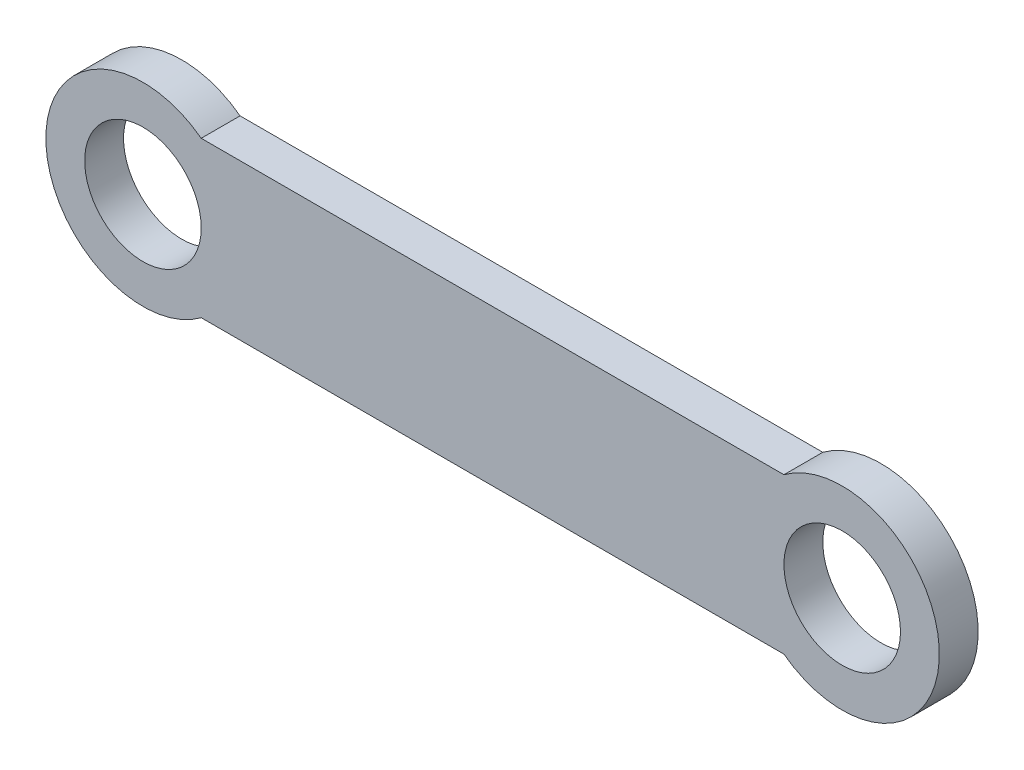
SolidWorks part; units mm, degrees
ref_plane "前视基准面" through (0, 0, 0) normal (0, 0, 1) x (1, 0, 0)
ref_plane "上视基准面" through (0, 0, 0) normal (0, 1, 0) x (1, 0, 0)
ref_plane "右视基准面" through (0, 0, 0) normal (1, 0, 0) x (0, 0, -1)
sketch "草图1" plane through (0, 0, 0) normal (0, 0, 1) x (1, 0, 0)
  line L1 (-29.9356, 0.5) -> (-14.9356, 0.5)
  line L3 (-29.9356, -3.5) -> (-14.9356, -3.5)
  arc A0 (-14.9356, -3.5) -> (-14.9356, 0.5) centre (-13.4356, -1.5) ccw
  arc A1 (-29.9356, 0.5) -> (-29.9356, -3.5) centre (-31.4356, -1.5) ccw
  circle A2 centre (-31.4356, -1.5) radius 1.5
  circle A3 centre (-13.4356, -1.5) radius 1.5
  point P0 (0, 0)
  dimension "D2" = 5
  dimension "D4" = 5
  dimension "D3" = 18
  dimension "D1" = 4
extrude "凸台-拉伸1" add sketch "草图1" along normal blind 1
